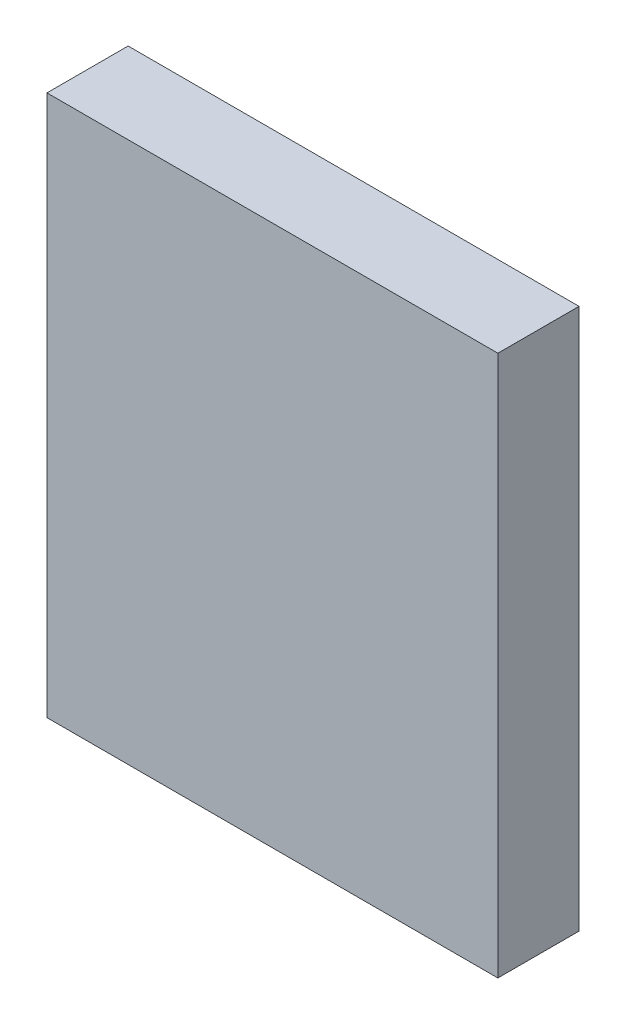
SolidWorks part; units mm, degrees
material "Balsa"
ref_plane "Front Plane" through (0, 0, 0) normal (0, 0, 1) x (1, 0, 0)
ref_plane "Top Plane" through (0, 0, 0) normal (0, 1, 0) x (1, 0, 0)
ref_plane "Right Plane" through (0, 0, 0) normal (1, 0, 0) x (0, 0, -1)
sketch "Sketch1" plane through (0, 0, 0) normal (0, 0, 1) x (1, 0, 0)
  line L1 (-50, 60) -> (50, 60)
  line L2 (-50, 60) -> (-50, -60)
  line L3 (-50, -60) -> (50, -60)
  line L4 (50, 60) -> (50, -60)
  line L5 (-50, 60) -> (50, -60) construction
  line L6 (-50, -60) -> (50, 60) construction
  point P0 (0, 0)
  dimension "D1" = 100
  dimension "D2" = 120
extrude "Boss-Extrude1" add sketch "Sketch1" along normal blind 18
